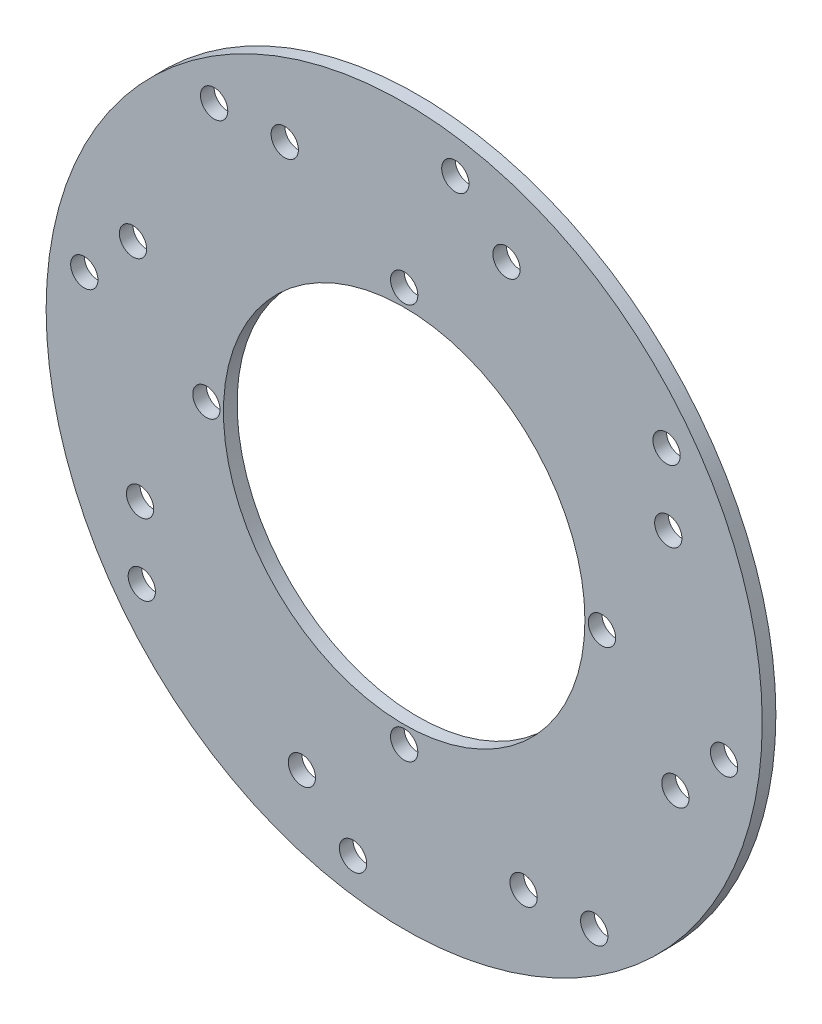
SolidWorks part; units mm, degrees
ref_plane "Front Plane" through (0, 0, 0) normal (0, 0, 1) x (1, 0, 0)
ref_plane "Top Plane" through (0, 0, 0) normal (0, 1, 0) x (1, 0, 0)
ref_plane "Right Plane" through (0, 0, 0) normal (1, 0, 0) x (0, 0, -1)
sketch "Sketch1" plane through (0, 0, 0) normal (0, 0, 1) x (1, 0, 0)
  line L0 (0, 0) -> (0, -50000) construction
  line L1 (4.9217, 0) -> (50004.9217, 0) construction
  line L2 (0, 0) -> (30, 79.5299) construction
  line L3 (0, 0) -> (15, 93.8083) construction
  circle A0 centre (0, 0) radius 105
  circle A1 centre (0, 0) radius 53
  circle A2 centre (0, 0) radius 58 construction
  circle A3 centre (0, 0) radius 95 construction
  circle A4 centre (0, 0) radius 85 construction
  circle A5 centre (0, 58) radius 4
  circle A6 centre (30, 79.5299) radius 4
  circle A7 centre (15, 93.8083) radius 4
  circle A8 centre (58, 0) radius 4
  circle A9 centre (0, -58) radius 4
  circle A10 centre (-58, 0) radius 4
  circle A11 centre (77.4493, 35.0229) radius 4
  circle A12 centre (79.5299, -30) radius 4
  circle A13 centre (35.0229, -77.4493) radius 4
  circle A14 centre (-30, -79.5299) radius 4
  circle A15 centre (-77.4493, -35.0229) radius 4
  circle A16 centre (-79.5299, 30) radius 4
  circle A17 centre (-35.0229, 77.4493) radius 4
  circle A18 centre (76.9391, 55.7259) radius 4
  circle A19 centre (93.8083, -15) radius 4
  circle A20 centre (55.7259, -76.9391) radius 4
  circle A21 centre (-15, -93.8083) radius 4
  circle A22 centre (-76.9391, -55.7259) radius 4
  circle A23 centre (-93.8083, 15) radius 4
  circle A24 centre (-55.7259, 76.9391) radius 4
  point P18 (-55.7931, 76.8904)
  point P19 (55.7259, -76.9391)
  dimension "D1" = 210
  dimension "D2" = 116
  dimension "D3" = 106
  dimension "D4" = 190
  dimension "D5" = 170
  dimension "D6" = 8
  dimension "D7" = 15
  dimension "D8" = 30
  dimension "D9" = 4
  dimension "D10" = 8
  dimension "D11" = 8
extrude "Boss-Extrude1" add sketch "Sketch1" along normal blind 4
